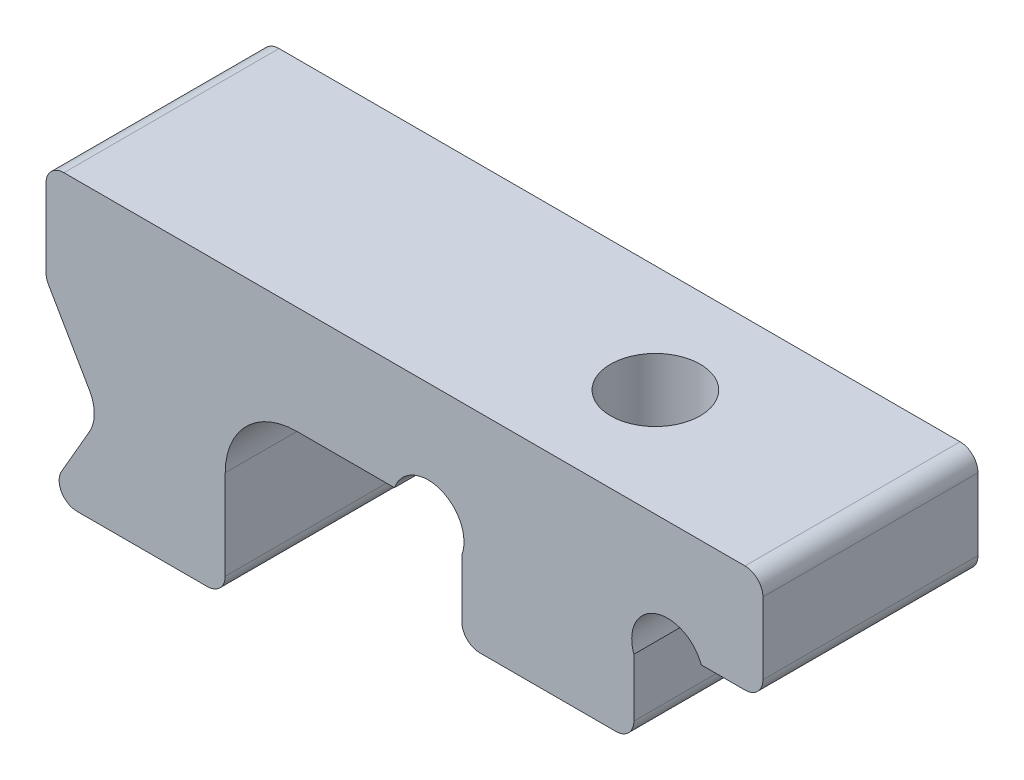
SolidWorks part; units mm, degrees
ref_plane "Plan de face" through (0, 0, 0) normal (0, 0, 1) x (1, 0, 0)
ref_plane "Plan de dessus" through (0, 0, 0) normal (0, 1, 0) x (1, 0, 0)
ref_plane "Plan de droite" through (0, 0, 0) normal (1, 0, 0) x (0, 0, -1)
sketch "Esquisse1" plane through (0, 0, 0) normal (0, 0, 1) x (1, 0, 0)
  line L0 (-6, 0) -> (-2.4, 0)
  line L1 (-2.4, -2.8) -> (2.4, -2.8)
  line L2 (-6, 0) -> (-6, 3)
  line L3 (-6, 3) -> (6, 3)
  line L4 (6, 0) -> (6, 3)
  line L5 (-6, 0) -> (6, 0) construction
  line L7 (-2.4, 0) -> (-2.4, -2.8)
  line L8 (6, 0) -> (2.4, 0)
  line L9 (2.4, 0) -> (2.4, -2.8)
  point P0 (0, 0)
  dimension "D1" = 12
  dimension "D2" = 4.8
  dimension "D3" = 3
  dimension "D4" = 2.8
extrude "Boss.-Extru.1" add sketch "Esquisse1" along normal mid plane 6
sketch "Esquisse2" plane through (0, 3, 0) normal (0, 1, 0) x (1, 0, 0)
  circle A0 centre (0, 0) radius 1.25
  dimension "D1" = 2.5
extrude "Enlèv. mat.-Extru.1" cut sketch "Esquisse2" against normal through all
sketch "Esquisse3" plane through (-6, 0, 0) normal (-1, 0, 0) x (0, 0, 1)
  line L1 (-3, 3) -> (3, 3)
  line L2 (-3, 3) -> (-3, 0)
  line L3 (-3, 0) -> (3, 0)
  line L4 (3, 3) -> (3, 0)
extrude "Boss.-Extru.2" add sketch "Esquisse3" along normal blind 8
sketch "Esquisse6" plane through (0, 0, 0) normal (0, -1, 0) x (1, 0, 0)
  line L0 (-14, -3) -> (-2.4, -3) construction
  line L1 (-14, 3) -> (-9, 3)
  line L2 (-14, 3) -> (-14, -3)
  line L3 (-14, -3) -> (-9, -3)
  line L4 (-9, 3) -> (-9, -3)
  dimension "D1" = 5
extrude "Boss.-Extru.4" add sketch "Esquisse6" along normal blind 5
sketch "Esquisse7" plane through (0, 0, 3) normal (0, 0, 1) x (1, 0, 0)
  line L0 (-14, 0.2) -> (-14, -5) construction
  line L1 (-14, 0.2) -> (-12.4989, -2.4)
  line L2 (-12.4989, -2.4) -> (-14, -5)
  line L3 (-14, 0.2) -> (-14, -5)
  line L6 (-9, 0) -> (-2.4, 0) construction
  point P6 (-14, -2.4)
  dimension "D1" = 120
  dimension "D2" = 2.4
extrude "Enlèv. mat.-Extru.3" cut sketch "Esquisse7" against normal through all
fillet "Congé2" radius 0.5 8 edges at (6, 3, 0) (-9, -5, 0) (6, 0, 0) (2.4, -2.8, 0) (-2.4, -2.8, 0) (-14, -5, 0) (-14, 3, 0) (-14, 0.2, 0)
fillet "Congé3" radius 2 1 edges at (-9, 0, 0)
fillet "Congé4" radius 1 1 edges at (-12.4989, -2.4, 0)
sketch "Esquisse9" plane through (0, 0, -3) normal (0, 0, -1) x (-1, 0, 0)
  line L1 (-4.2794, 0) -> (-2.4, -0.684)
  line L2 (-2.4, 0) -> (-5.5, 0) construction
  line L3 (-2.4, -2.3) -> (-2.4, 0) construction
  line L4 (0, 3.3) -> (0, -3.3) construction
  line L5 (4.2794, 0) -> (2.4, -0.684)
  arc A0 (-4.2794, 0) -> (-2.4, -0.684) centre (-3.3397, -0.342) cw
  arc A1 (4.2794, 0) -> (2.4, -0.684) centre (3.3397, -0.342) ccw
  dimension "D1" = 1
  dimension "D2" = 70
extrude "Enlèv. mat.-Extru.4" cut sketch "Esquisse9" against normal through all
